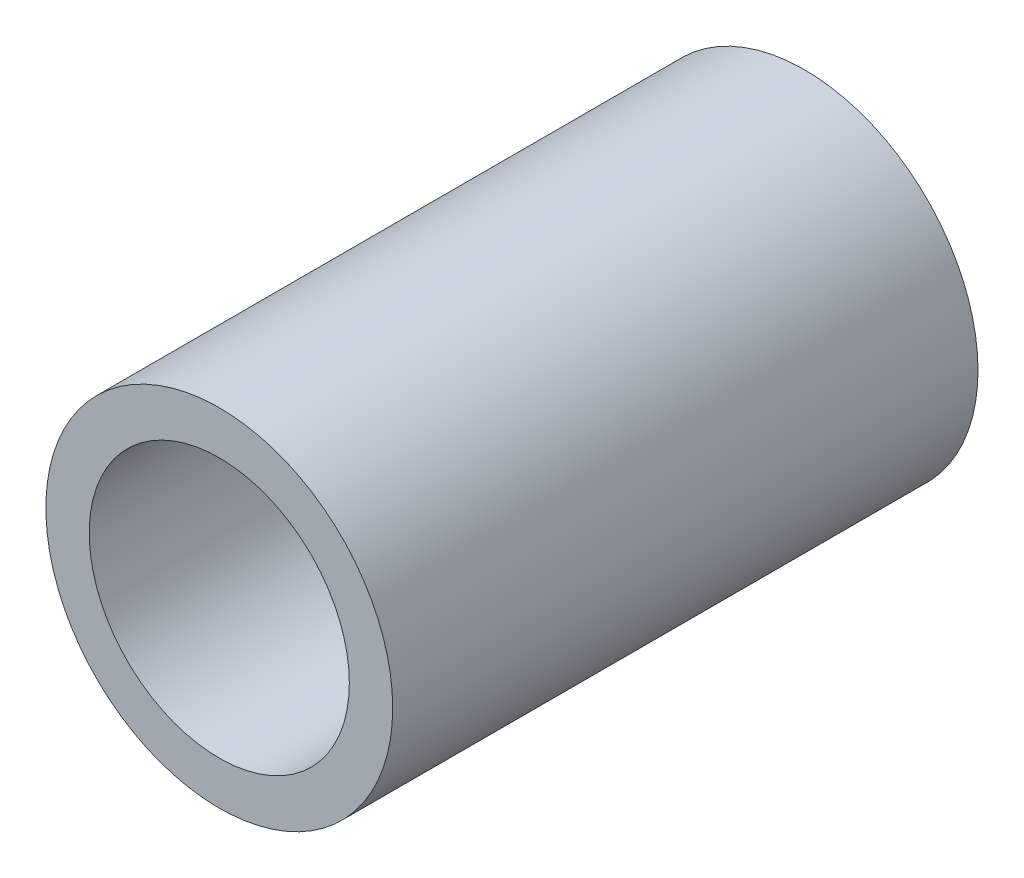
SolidWorks part; units mm, degrees
ref_plane "Front Plane" through (0, 0, 0) normal (0, 0, 1) x (1, 0, 0)
ref_plane "Top Plane" through (0, 0, 0) normal (0, 1, 0) x (1, 0, 0)
ref_plane "Right Plane" through (0, 0, 0) normal (1, 0, 0) x (0, 0, -1)
sketch "Sketch1" plane through (0, 0, 0) normal (0, 0, 1) x (1, 0, 0)
  circle A0 centre (0, 0) radius 3.175
  circle A1 centre (0, 0) radius 4.2333
  dimension "D1" = 6.35
  dimension "D2" = 8.4667
extrude "Boss-Extrude1" add sketch "Sketch1" along normal blind 14.2875
